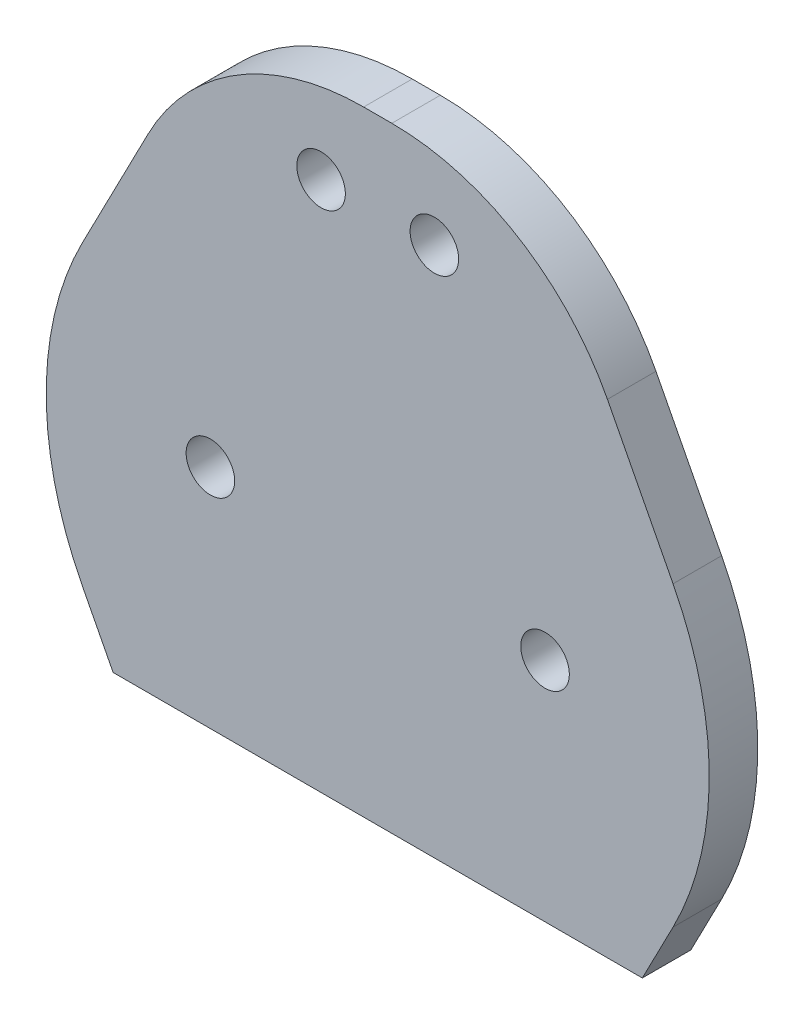
SolidWorks part; units mm, degrees
material "3.0205 (EN-AW 1200)"
ref_plane "Piano frontale" through (0, 0, 0) normal (0, 0, 1) x (1, 0, 0)
ref_plane "Piano superiore" through (0, 0, 0) normal (0, 1, 0) x (1, 0, 0)
ref_plane "Piano destro" through (0, 0, 0) normal (1, 0, 0) x (0, 0, -1)
sketch "Schizzo1" plane through (0, 0, 0) normal (0, 0, 1) x (1, 0, 0)
  line L0 (-54.8681, 0) -> (41.6416, 0) construction
  line L1 (0, 0) -> (-6.8404, 18.7939) construction
  line L2 (-10.3404, -25.7598) -> (-10.3404, 32.5728) construction
  line L3 (12.6596, 24) -> (12.6596, -14)
  line L4 (-13.8404, 18.7939) -> (-20.6808, 0) construction
  line L6 (12.6596, -14) -> (-33.3404, -14)
  line L7 (-33.3404, -14) -> (-33.3404, 24)
  line L8 (-33.3404, 24) -> (12.6596, 24)
  circle A0 centre (-6.8404, 18.7939) radius 1.5
  circle A1 centre (0, 0) radius 1.5
  circle A2 centre (-20.6808, 0) radius 1.5
  circle A3 centre (-13.8404, 18.7939) radius 1.5
  dimension "D6" = 38
  dimension "D3" = 3
  dimension "D5" = 3
  dimension "D7" = 24
  dimension "D1" = 20
  dimension "D2" = 70
  dimension "D4" = 46
  dimension "D8" = 7
  dimension "D9" = 23
extrude "Estrusione-Estrusione3" add sketch "Schizzo1" along normal blind 3
sketch "Schizzo4" plane through (0, 0, 3) normal (0, 0, 1) x (1, 0, 0)
  line L0 (-10.3404, 24) -> (-20.3404, 24)
  line L1 (12.6596, 24) -> (-33.3404, 24) construction
  line L2 (-20.3404, 24) -> (-33.3404, -1.1396)
  line L3 (-33.3404, 24) -> (-33.3404, -14) construction
  line L4 (-33.3404, -1.1396) -> (-26.6901, -14)
  line L5 (-33.3404, -14) -> (12.6596, -14) construction
  line L6 (-26.6901, -14) -> (6.0093, -14)
  line L7 (6.0093, -14) -> (12.6596, -1.1396)
  line L8 (12.6596, -14) -> (12.6596, 24) construction
  line L9 (12.6596, -1.1396) -> (-0.3404, 24)
  line L10 (-0.3404, 24) -> (-20.3404, 24)
  line M8 (-33.3404, -14) -> (12.6596, -14)
  line M9 (12.6596, -14) -> (12.6596, 24)
  line M10 (12.6596, 24) -> (-33.3404, 24)
  line M11 (-33.3404, 24) -> (-33.3404, -14)
  dimension "D1" = 10
  dimension "D2" = 28.3019
  dimension "D3" = 10
extrude "Taglio-Estrusione1" cut sketch "Schizzo4" against normal blind 3 contours L2 M10 M11 | L9 M9 M10 | L4 M11 M8 | L7 M8 M9
fillet "Raccordo1" radius 15 1 edges at (-0.3404, 24, 1.5)
fillet "Raccordo2" radius 15 1 edges at (-20.3404, 24, 1.5)
fillet "Raccordo3" radius 20 1 edges at (12.6596, -1.1396, 1.5)
fillet "Raccordo4" radius 20 1 edges at (-33.3404, -1.1396, 1.5)
